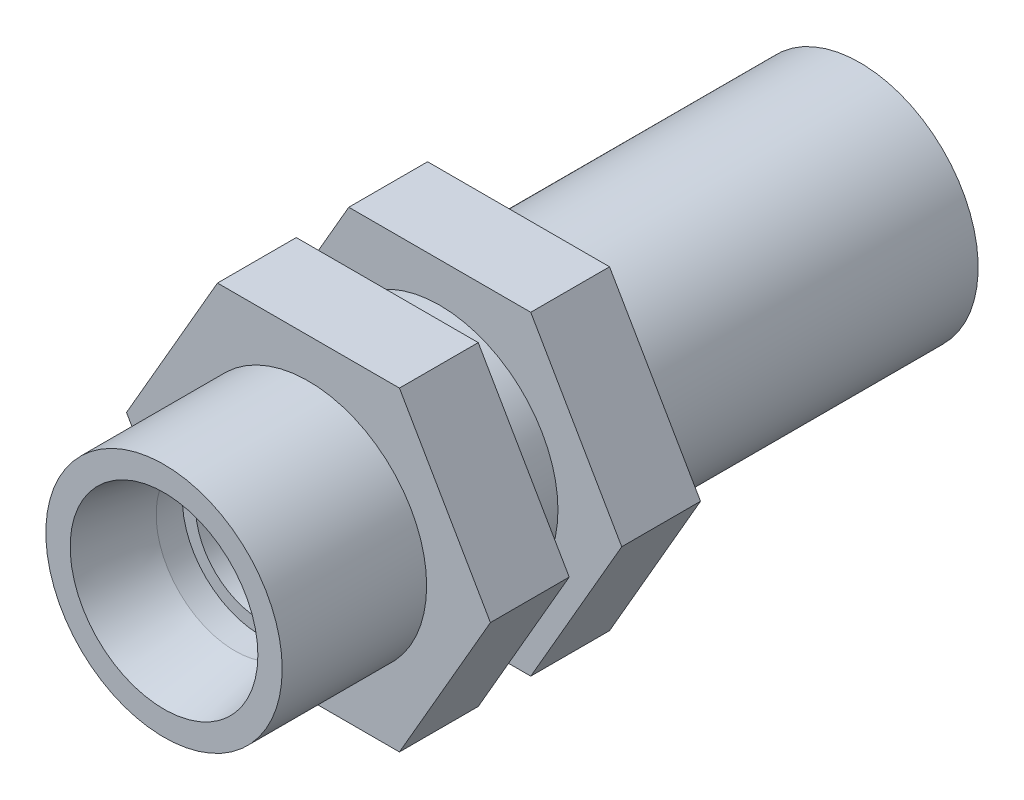
SolidWorks part; units mm, degrees
ref_plane "Plane1" through (0, 0, 0) normal (0, 0, 1) x (1, 0, 0)
ref_plane "Plane2" through (0, 0, 0) normal (0, 1, 0) x (1, 0, 0)
ref_plane "Plane3" through (0, 0, 0) normal (1, 0, 0) x (0, 0, -1)
sketch "Sketch1" plane through (0, 0, 0) normal (0, 0, 1) x (1, 0, 0)
  line L1 (13.8564, 0) -> (6.9282, 12)
  line L2 (6.9282, 12) -> (-6.9282, 12)
  line L3 (-6.9282, 12) -> (-13.8564, 0)
  line L4 (-13.8564, 0) -> (-6.9282, -12)
  line L5 (-6.9282, -12) -> (6.9282, -12)
  line L6 (6.9282, -12) -> (13.8564, 0)
  circle A0 centre (0, 0) radius 12 construction
extrude "Base-Extrude" add sketch "Sketch1" along normal blind 6
sketch "Sketch2" plane through (0, 0, 6) normal (0, 0, 1) x (1, 0, 0)
  circle A0 centre (0, 0) radius 9
extrude "Boss-Extrude1" add sketch "Sketch2" along normal blind 11
sketch "Sketch3" plane through (0, 0, 0) normal (0, 0, -1) x (-1, 0, 0)
  circle A0 centre (0, 0) radius 9
extrude "Boss-Extrude2" add sketch "Sketch3" along normal blind 4
sketch "Sketch4" plane through (0, 0, -4) normal (0, 0, -1) x (-1, 0, 0)
  line L1 (13.8564, 0) -> (6.9282, 12)
  line L2 (6.9282, 12) -> (-6.9282, 12)
  line L3 (-6.9282, 12) -> (-13.8564, 0)
  line L4 (-13.8564, 0) -> (-6.9282, -12)
  line L5 (-6.9282, -12) -> (6.9282, -12)
  line L6 (6.9282, -12) -> (13.8564, 0)
  circle A0 centre (0, 0) radius 12 construction
extrude "Boss-Extrude3" add sketch "Sketch4" along normal blind 6
sketch "Sketch5" plane through (0, 0, -10) normal (0, 0, -1) x (-1, 0, 0)
  circle A0 centre (0, 0) radius 9
extrude "Boss-Extrude4" add sketch "Sketch5" along normal blind 26
sketch "Sketch8" plane through (0, 0, 0) normal (1, 0, 0) x (0, 0, -1)
  line L0 (-19, 0) -> (40, 0) construction
  line L1 (36, -9) -> (36, 9) construction
  line L2 (36, 0) -> (36, 7.1478)
  line L3 (-17, 9) -> (-17, -9) construction
  line L4 (-17, 7.1478) -> (-17, 0)
  line L5 (-17, 7.1478) -> (-11.6, 6)
  line L6 (-11.6, 6) -> (-9.6, 6)
  line L7 (-9.6, 6) -> (-9.6, 5)
  line L8 (36, 7.1478) -> (30.6, 6)
  line L9 (30.6, 6) -> (28.6, 6)
  line L10 (28.6, 6) -> (28.6, 5)
  line L11 (-9.6, 5) -> (28.6, 5)
  line L12 (36, 0) -> (-17, 0)
  dimension "D1" = 12
  dimension "Indv. dia. 2" = 12
  dimension "D2" = 2
  dimension "D5" = 2
  dimension "D6" = 12
  dimension "Indv. dia. 1" = 10
revolve "Cut-Revolve1" cut sketch "Sketch8" angle 360 about L0
